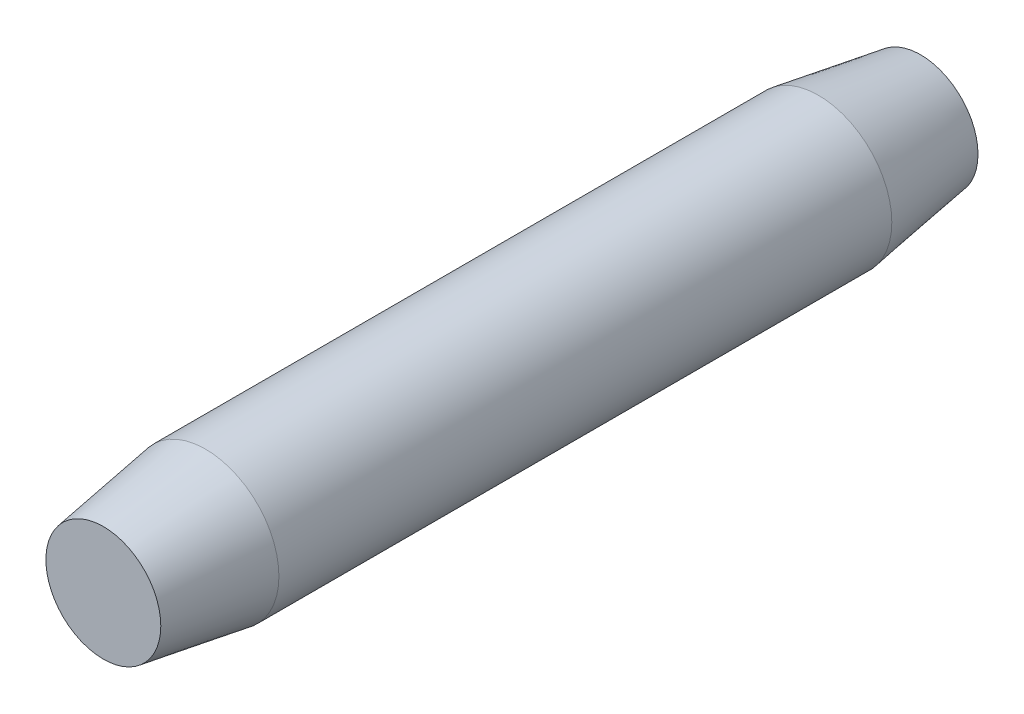
SolidWorks part; units mm, degrees
material "6061-T6 (SS)"
ref_plane "Front Plane" through (0, 0, 0) normal (0, 0, 1) x (1, 0, 0)
ref_plane "Top Plane" through (0, 0, 0) normal (0, 1, 0) x (1, 0, 0)
ref_plane "Right Plane" through (0, 0, 0) normal (1, 0, 0) x (0, 0, -1)
sketch "Sketch1" plane through (0, 0, 0) normal (0, 0, 1) x (1, 0, 0)
  circle A0 centre (0, 0) radius 18.2563
  dimension "D1" = 36.5125
extrude "Boss-Extrude1" add sketch "Sketch1" along normal mid plane 203.2
chamfer "Chamfer1" distance 25.4 distance2 3.9688 1 edges at (18.2563, 0, 101.6)
chamfer "Chamfer2" distance 3.9688 distance2 25.4 1 edges at (18.2563, 0, -101.6)
